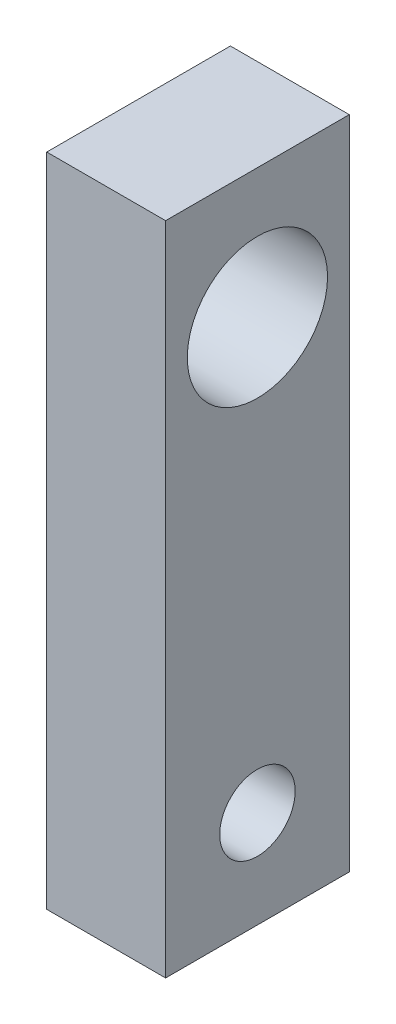
SolidWorks part; units mm, degrees
ref_plane "Front Plane" through (0, 0, 0) normal (0, 0, 1) x (1, 0, 0)
ref_plane "Top Plane" through (0, 0, 0) normal (0, 1, 0) x (1, 0, 0)
ref_plane "Right Plane" through (0, 0, 0) normal (1, 0, 0) x (0, 0, -1)
sketch "Sketch5" plane through (0, 0, 0) normal (1, 0, 0) x (0, 0, -1)
  line L0 (2.835, 0) -> (2.835, 3) construction
  line L1 (0, 0) -> (5.67, 0)
  line L2 (0, 0) -> (0, 20.25)
  line L3 (0, 20.25) -> (5.67, 20.25)
  line L4 (5.67, 0) -> (5.67, 20.25)
  line L5 (2.835, 3) -> (2.835, 10) construction
  line L6 (2.835, 10) -> (2.835, 11) construction
  line L7 (2.835, 11) -> (2.835, 16.25) construction
  line L8 (2.835, 16.25) -> (2.835, 20.25) construction
  circle A0 centre (2.835, 3) radius 1.165
  circle A1 centre (2.835, 16.25) radius 2.165
  dimension "D7" = 4.33
  dimension "D8" = 2.33
  dimension "D1" = 5.67
  dimension "D2" = 3
  dimension "D3" = 10
  dimension "D4" = 4
  dimension "D5" = 5.25
  dimension "D6" = 1
extrude "Boss-Extrude2" add sketch "Sketch5" along normal blind 3.67
equation "\"post_length\"=6"
equation "\"post_width\"= 4"
equation "\"post_height\"=13"
equation "\"pin_offset\"= 3"
equation "\"pin_dia\"=2"
equation "\"pin_dist_from_top\"=4"
equation "\"D1@Sketch5\"=\"post_length\"-\"tol\""
equation "\"D2@Sketch5\"=\"pin_offset\""
equation "\"pin_depth\"= 10"
equation "\"D3@Sketch5\"=\"pin_depth\""
equation "\"D4@Sketch5\"=\"pin_dist_from_top\""
equation "\"pin_bearing_OD\"= 10.5"
equation "\"D5@Sketch5\"=\"pin_bearing_OD\"/2"
equation "\"post_clearance\"=1"
equation "\"D6@Sketch5\"=\"post_clearance\""
equation "\"bearing_pin_dia\"=4"
equation "\"D7@Sketch5\"=\"bearing_pin_dia\"+\"tol\""
equation "\"D8@Sketch5\"=\"pin_dia\"+\"tol\""
equation "\"D1@Boss-Extrude2\"=\"post_width\"-\"tol\""
equation "\"tol\" = 0.33"
